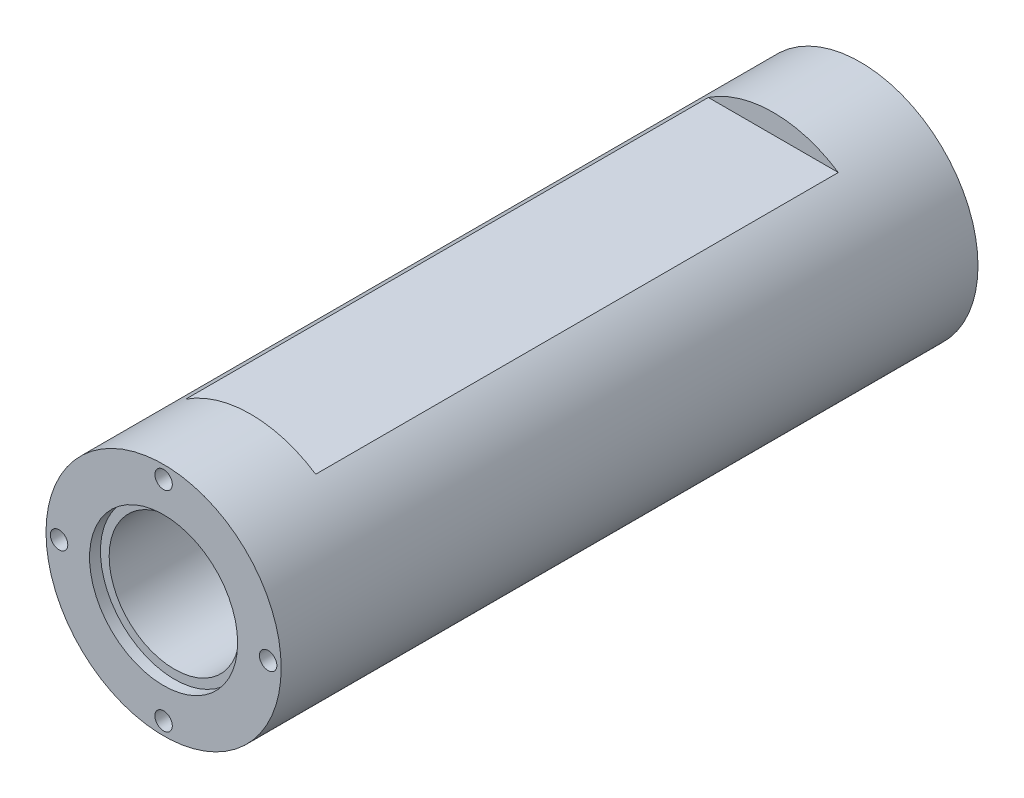
SolidWorks part; units mm, degrees
ref_plane "Plan de face" through (0, 0, 0) normal (0, 0, 1) x (1, 0, 0)
ref_plane "Plan de dessus" through (0, 0, 0) normal (0, 1, 0) x (1, 0, 0)
ref_plane "Plan de droite" through (0, 0, 0) normal (1, 0, 0) x (0, 0, -1)
sketch "Esquisse1" plane through (0, 0, 0) normal (0, 0, 1) x (1, 0, 0)
  circle A0 centre (0, 0) radius 15
  circle A1 centre (0, 0) radius 27
extrude "Extrusion1" add sketch "Esquisse1" along normal blind 160
sketch "Esquisse2" plane through (0, 0, 160) normal (0, 0, 1) x (1, 0, 0)
  line L0 (0, 0) -> (0, 24) construction
  circle A0 centre (0, 24) radius 2
  circle A1 centre (24, 0) radius 2
  circle A2 centre (0, -24) radius 2
  circle A3 centre (-24, 0) radius 2
extrude "Extrusion2" cut sketch "Esquisse2" against normal blind 15
sketch "Esquisse3" plane through (0, 0, 0) normal (0, 0, -1) x (-1, 0, 0)
  line L0 (0, 0) -> (0, 24) construction
  circle A0 centre (0, 24) radius 2
  circle A1 centre (24, 0) radius 2
  circle A2 centre (0, -24) radius 2
  circle A3 centre (-24, 0) radius 2
extrude "Extrusion3" cut sketch "Esquisse3" against normal blind 15
sketch "Esquisse4" plane through (0, 0, 160) normal (0, 0, 1) x (1, 0, 0)
  circle A0 centre (0, 0) radius 17
  circle A1 centre (0, 0) radius 15
extrude "Extrusion4" cut sketch "Esquisse4" against normal blind 2.5
sketch "Esquisse5" plane through (0, 0, 0) normal (0, 0, -1) x (-1, 0, 0)
  circle A0 centre (0, 0) radius 17
  circle A1 centre (0, 0) radius 15
extrude "Extrusion5" cut sketch "Esquisse5" against normal blind 2.5
sketch "Esquisse6" plane through (0, 0, 0) normal (1, 0, 0) x (0, 0, -1)
  line L0 (-20, 27) -> (-140, 27)
  line L1 (-160, -27) -> (0, -27) construction
  line L2 (-140, -21) -> (-20, -21)
  line L3 (-20, -21) -> (-20, -27)
  line L4 (-140, -21) -> (-140, -27)
  line L5 (-20, -27) -> (-140, -27)
  line L6 (-160, 0) -> (-112.7212, 0) construction
  line L7 (-160, 27) -> (-160, -27) construction
  line L8 (-140, 22.5) -> (-140, 27)
  line L9 (-20, 22.5) -> (-20, 27)
  line L11 (-140, 22.5) -> (-20, 22.5)
extrude "Extrusion6" cut sketch "Esquisse6" against normal through all and the other way through all
